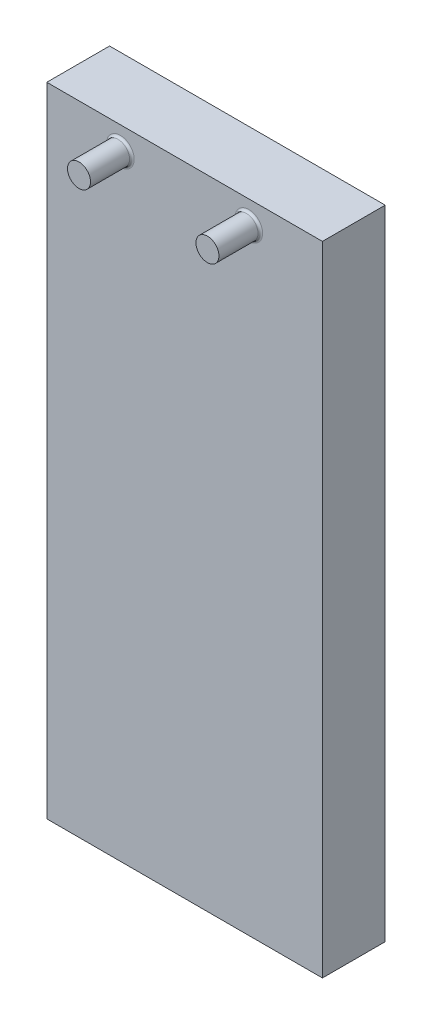
SolidWorks part; units mm, degrees
ref_plane "Front Plane" through (0, 0, 0) normal (0, 0, 1) x (1, 0, 0)
ref_plane "Top Plane" through (0, 0, 0) normal (0, 1, 0) x (1, 0, 0)
ref_plane "Right Plane" through (0, 0, 0) normal (1, 0, 0) x (0, 0, -1)
sketch "Sketch1" plane through (0, 0, 0) normal (0, 1, 0) x (1, 0, 0)
  line L1 (-59.92, -13.65) -> (59.92, -13.65)
  line L2 (-59.92, -13.65) -> (-59.92, 13.65)
  line L3 (-59.92, 13.65) -> (59.92, 13.65)
  line L4 (59.92, -13.65) -> (59.92, 13.65)
  line L5 (-59.92, -13.65) -> (59.92, 13.65) construction
  line L6 (-59.92, 13.65) -> (59.92, -13.65) construction
  point P0 (0, 0)
  dimension "D1" = 119.84
  dimension "D2" = 27.3
extrude "Boss-Extrude1" add sketch "Sketch1" along normal blind 277.37
sketch "Sketch2" plane through (0, 0, 13.65) normal (0, 0, 1) x (1, 0, 0)
  line L0 (-59.92, 257.37) -> (59.92, 257.37)
  line L1 (-59.92, 277.37) -> (-59.92, 0) construction
  line L2 (59.92, 277.37) -> (59.92, 0) construction
  line L3 (-59.92, 277.37) -> (59.92, 277.37) construction
  line L4 (-59.92, 257.37) -> (-59.92, 277.37)
  line L5 (-59.92, 267.37) -> (59.92, 267.37) construction
  circle A2 centre (-27.92, 267.37) radius 5
  circle A3 centre (27.92, 267.37) radius 5
  dimension "D4" = 10
  dimension "D1" = 20
  dimension "D2" = 32
  dimension "D3" = 32
extrude "Boss-Extrude2" add sketch "Sketch2" along normal blind 18 contours L5 A3 | A3 L5 | L5 A2 | A2 L5
fillet "Fillet1" radius 1 2 edges at (22.92, 267.37, 13.65) (-32.92, 267.37, 13.65)
equation "\"PCWidth\"= 340mm'Distance of longest part parallel to GPU(ussually GPU)"
equation "\"PCLength\"= 143mm'Length across I/O from PS to GPU"
equation "\"PCHeight\"= 190mm'Tallest point with mobo laying flat"
equation "\"WallThickness\"= 9mm'Thickness of each outer tank wall"
equation "\"ThermoBarrierThickness\"= 6mm'Thickness of barrier between hot side and cold side"
equation "\"HotSideGap\"= 15mm'Space in the hot side that hot fluid flows into"
equation "\"PCClearance\"= 40mm'Clearance from top of tank to top of PC"
equation "\"RadiatorHeight\"= 277.37mm'Final Height from ground of radiators"
equation "\"D1@Boss-Extrude1\"=\"RadiatorHeight\""
